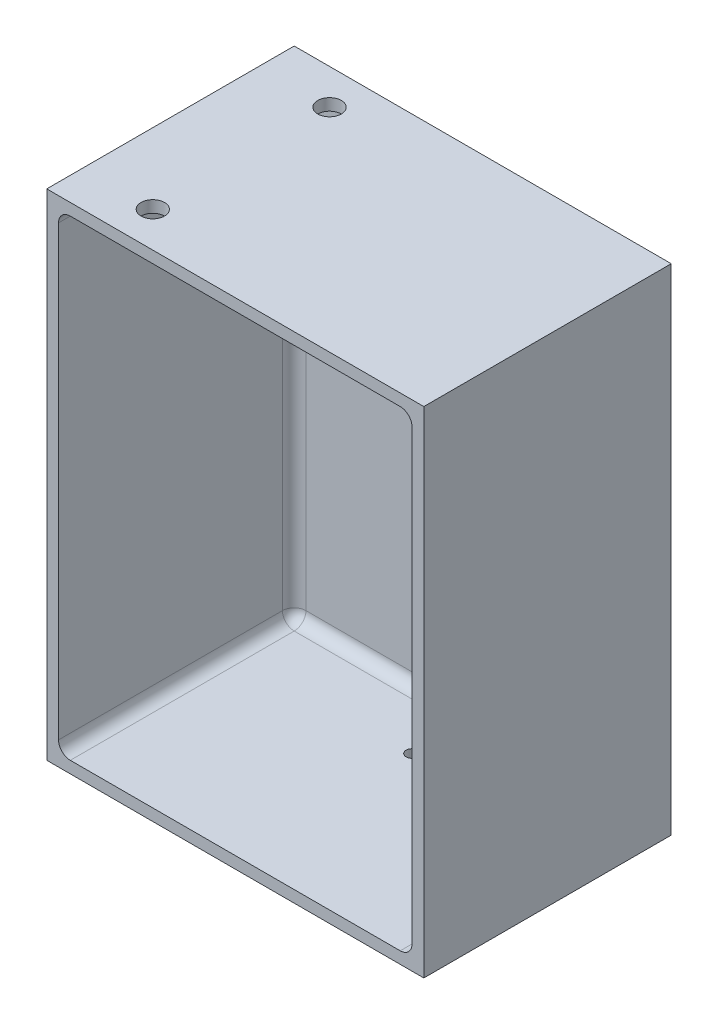
SolidWorks part; units mm, degrees
ref_plane "Front Plane" through (0, 0, 0) normal (0, 0, 1) x (1, 0, 0)
ref_plane "Top Plane" through (0, 0, 0) normal (0, 1, 0) x (1, 0, 0)
ref_plane "Right Plane" through (0, 0, 0) normal (1, 0, 0) x (0, 0, -1)
sketch "Sketch1" plane through (0, 0, 0) normal (0, 0, 1) x (1, 0, 0)
  line L0 (-80, 105) -> (-80, -105)
  line L1 (75, 100) -> (-75, 100)
  line L2 (75, 100) -> (75, -100)
  line L3 (75, -100) -> (-75, -100)
  line L4 (-75, 100) -> (-75, -100)
  line L5 (75, 100) -> (-75, -100) construction
  line L6 (75, -100) -> (-75, 100) construction
  line L7 (80, -105) -> (-80, -105)
  line L8 (80, 105) -> (80, -105)
  line L9 (80, 105) -> (-80, 105)
  point P0 (0, 0)
  dimension "D1" = 200
  dimension "D2" = 150
  dimension "D3" = 5
extrude "Boss-Extrude1" add sketch "Sketch1" along normal blind 100
sketch "Sketch3" plane through (0, 0, 0) normal (0, 0, -1) x (-1, 0, 0)
  line L0 (80, -105) -> (-80, -105) construction
  line L1 (80, 105) -> (80, -105) construction
  line L2 (-80, 105) -> (80, 105) construction
  line L3 (-80, -105) -> (-80, 105) construction
  line L4 (80, -105) -> (-80, -105)
  line L5 (80, 105) -> (80, -105)
  line L6 (-80, 105) -> (80, 105)
  line L7 (-80, -105) -> (-80, 105)
extrude "Boss-Extrude2" add sketch "Sketch3" along normal blind 5
fillet "Fillet1" radius 5 8 edges at (75, 0, 0) (0, -100, 0) (-75, 0, 0) (0, 100, 0) (-75, 100, 50) (-75, -100, 50) (75, -100, 50) (75, 100, 50)
sketch "Sketch4" plane through (0, 105, 0) normal (0, 1, 0) x (1, 0, 0)
  line L0 (-80, 5) -> (80, 5) construction
  line L1 (80, -100) -> (-80, -100) construction
  line L2 (-80, -100) -> (-80, 5) construction
  circle A0 centre (-50, -10) radius 5
  circle A1 centre (-50, -85) radius 5
  dimension "D1" = 10
  dimension "D2" = 10
  dimension "D4" = 15
  dimension "D5" = 30
  dimension "D6" = 30
  dimension "D3" = 15
extrude "Cut-Extrude1" cut sketch "Sketch4" against normal blind 48
sketch "Sketch5" plane through (0, -105, 0) normal (0, -1, 0) x (1, 0, 0)
  line L0 (80, -5) -> (-80, -5) construction
  line L1 (80, 100) -> (80, -5) construction
  circle A0 centre (0, 25) radius 2.5
  dimension "D1" = 5
  dimension "D3" = 80
  dimension "D2" = 30
extrude "Cut-Extrude2" cut sketch "Sketch5" against normal blind 40
